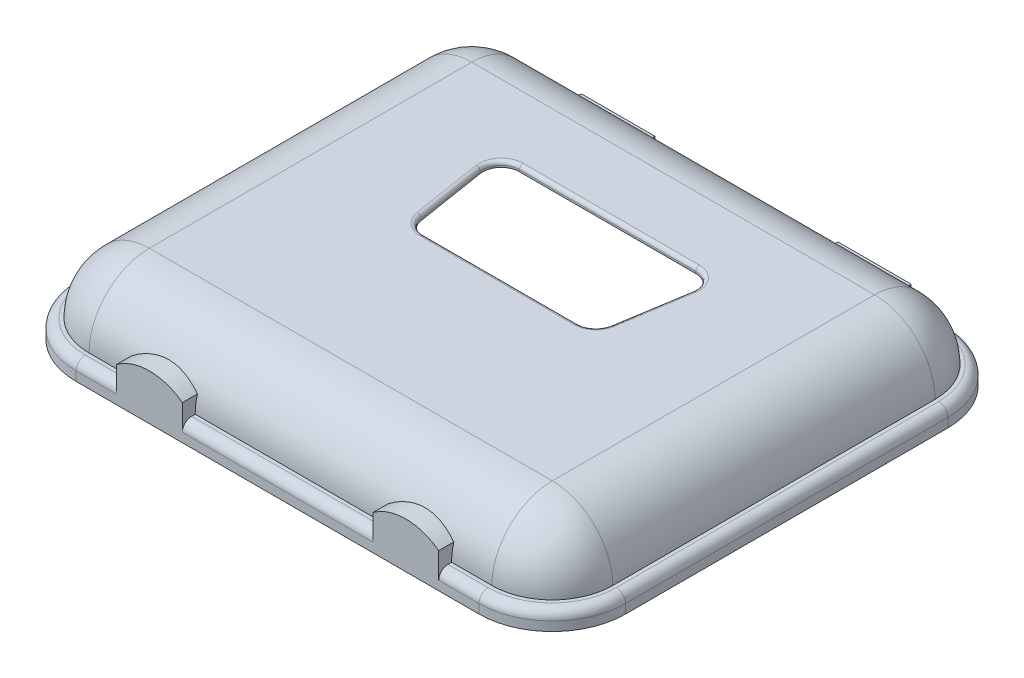
SolidWorks part; units mm, degrees
ref_plane "Front Plane" through (0, 0, 0) normal (0, 0, 1) x (1, 0, 0)
ref_plane "Top Plane" through (0, 0, 0) normal (0, 1, 0) x (1, 0, 0)
ref_plane "Right Plane" through (0, 0, 0) normal (1, 0, 0) x (0, 0, -1)
sketch "Sketch1" plane through (0, 0, 0) normal (0, 1, 0) x (1, 0, 0)
  line L1 (-118.56, 82.94) -> (167.44, 82.94)
  line L2 (-118.56, 82.94) -> (-118.56, -159.06)
  line L3 (-118.56, -159.06) -> (167.44, -159.06)
  line L4 (167.44, 82.94) -> (167.44, -159.06)
  dimension "D1" = 286
  dimension "D2" = 242
extrude "Boss-Extrude1" add sketch "Sketch1" along normal blind 43 contours L2 L3 L4 L1
fillet "Fillet1" radius 33 8 edges at (167.44, 43, 38.06) (24.44, 43, 159.06) (-118.56, 43, 38.06) (24.44, 43, -82.94) (167.44, 21.5, -82.94) (-118.56, 21.5, -82.94) (-118.56, 21.5, 159.06) (167.44, 21.5, 159.06)
shell "Shell1" thickness 3
sketch "Sketch2" plane through (0, 0, 0) normal (0, -1, 0) x (1, 0, 0)
  line L0 (-85.56, 159.06) -> (134.44, 159.06) construction
  line L1 (-85.56, 166.06) -> (134.44, 166.06)
  line L2 (-125.56, 126.06) -> (-125.56, -49.94)
  line L3 (-85.56, -89.94) -> (134.44, -89.94)
  line L4 (174.44, 126.06) -> (174.44, -49.94)
  line L5 (-118.56, -49.94) -> (-118.56, 126.06) construction
  line L6 (167.44, -49.94) -> (167.44, 126.06) construction
  line L7 (-85.56, -82.94) -> (134.44, -82.94) construction
  line L9 (-85.56, 159.06) -> (134.44, 159.06)
  line L10 (-118.56, 126.06) -> (-118.56, -49.94)
  line L11 (-85.56, -82.94) -> (134.44, -82.94)
  line L12 (167.44, 126.06) -> (167.44, -49.94)
  arc A0 (134.44, -89.94) -> (174.44, -49.94) centre (134.44, -49.94) ccw
  arc A1 (-125.56, -49.94) -> (-85.56, -89.94) centre (-85.56, -49.94) ccw
  arc A2 (134.44, 166.06) -> (174.44, 126.06) centre (134.44, 126.06) cw
  arc A3 (-85.56, 166.06) -> (-125.56, 126.06) centre (-85.56, 126.06) ccw
  arc A4 (-118.56, -49.94) -> (-85.56, -82.94) centre (-85.56, -49.94) ccw
  arc A5 (134.44, -82.94) -> (167.44, -49.94) centre (134.44, -49.94) ccw
  arc A6 (134.44, 159.06) -> (167.44, 126.06) centre (134.44, 126.06) cw
  arc A7 (-85.56, 159.06) -> (-118.56, 126.06) centre (-85.56, 126.06) ccw
  dimension "D5" = 40
  dimension "D6" = 33
  dimension "D1" = 7
  dimension "D2" = 7
  dimension "D3" = 7
  dimension "D4" = 7
extrude "Boss-Extrude2" add sketch "Sketch2" against normal blind 10
fillet "Fillet2" radius 5 8 edges at (162.7243, 10, 154.3443) (174.44, 10, 38.06) (162.7243, 10, -78.2243) (24.44, 10, -89.94) (-113.8443, 10, -78.2243) (-125.56, 10, 38.06) (-113.8443, 10, 154.3443) (24.44, 10, 166.06)
sketch "Sketch4" plane through (0, 43, 0) normal (0, 1, 0) x (1, 0, 0)
  line L0 (24.44, 14.14) -> (24.44, -44.26) construction
  line L1 (-23.6848, 14.14) -> (72.5648, 14.14)
  line L2 (-33.56, 2.5649) -> (-27.4352, -35.8351)
  line L3 (-17.56, -44.26) -> (66.44, -44.26)
  line L4 (82.44, 2.5649) -> (76.3152, -35.8351)
  line L6 (-27.4352, -35.8351) -> (76.3152, -35.8351) construction
  line L7 (24.44, -126.06) -> (24.44, 49.94) construction
  line L8 (-85.56, -126.06) -> (134.44, -126.06) construction
  line L9 (134.44, 49.94) -> (-85.56, 49.94) construction
  line L10 (-85.56, 89.94) -> (134.44, 89.94) construction
  arc A0 (-27.4352, -35.8351) -> (-17.56, -44.26) centre (-17.56, -34.26) ccw
  arc A1 (66.44, -44.26) -> (76.3152, -35.8351) centre (66.44, -34.26) ccw
  arc A2 (72.5648, 14.14) -> (82.44, 2.5649) centre (72.5648, 4.14) cw
  arc A3 (-23.6848, 14.14) -> (-33.56, 2.5649) centre (-23.6848, 4.14) ccw
  point P13 (-26.0914, -44.26)
  point P16 (74.9714, -44.26)
  point P19 (84.2862, 14.14)
  point P22 (-35.4062, 14.14)
  dimension "D4" = 10
  dimension "D1" = 84
  dimension "D2" = 116
  dimension "D3" = 58.4
  dimension "D5" = 75.8
extrude "Cut-Extrude2" cut sketch "Sketch4" against normal through all
fillet "Fillet3" radius 2 8 edges at (-24.0503, 43, 41.8676) (-30.4976, 43, 16.6351) (-31.2924, 43, -10.6303) (24.44, 43, -14.14) (80.1724, 43, -10.6303) (79.3776, 43, 16.6351) (72.9303, 43, 41.8676) (24.44, 43, 44.26)
sketch "Sketch5" plane through (0, 0, -89.94) normal (0, 0, -1) x (-1, 0, 0)
  line L0 (85.56, 0) -> (-134.44, 0) construction
  line L1 (-114.44, 0) -> (-74.44, 0)
  line L2 (-114.44, 0) -> (-114.44, 18)
  line L3 (-114.44, 18) -> (-74.44, 18)
  line L4 (-74.44, 0) -> (-74.44, 18)
  line L5 (-94.44, 18) -> (45.56, 18) construction
  line L6 (25.56, 0) -> (65.56, 0)
  line L7 (25.56, 0) -> (25.56, 18)
  line L8 (25.56, 18) -> (65.56, 18)
  line L9 (65.56, 0) -> (65.56, 18)
  line L10 (-24.44, 18) -> (-24.44, 0) construction
  dimension "D1" = 40
  dimension "D2" = 140
  dimension "D3" = 18
extrude "Boss-Extrude3" add sketch "Sketch5" against normal up to next
sketch "Sketch6" plane through (0, 0, 166.06) normal (0, 0, 1) x (1, 0, 0)
  line L0 (134.44, 0) -> (-85.56, 0) construction
  line L1 (-27.56, 0) -> (-63.56, 0)
  line L2 (-27.56, 0) -> (-27.56, 25)
  line L3 (-27.56, 25) -> (-63.56, 25)
  line L4 (-63.56, 0) -> (-63.56, 25)
  line L5 (-45.56, 25) -> (94.44, 25) construction
  line L6 (76.44, 0) -> (112.44, 0)
  line L7 (76.44, 0) -> (76.44, 25)
  line L8 (76.44, 25) -> (112.44, 25)
  line L9 (112.44, 0) -> (112.44, 25)
  line L10 (24.44, 25) -> (24.44, 0) construction
  circle A0 centre (-45.56, -5) radius 30
  circle A1 centre (94.44, -5) radius 30
  point P16 (-45.0908, 28.8434)
  point P17 (-40.3936, -6.9829)
  point P20 (94.44, -8.6059)
  point P21 (94.44, -2)
  point P22 (72.9767, -2)
  line M2 (134.44, 5) -> (-85.56, 5)
  line M4 (-85.56, 0) -> (134.44, 0)
  dimension "D4" = 60
  dimension "D1" = 140
  dimension "D2" = 36
  dimension "D3" = 25
extrude "Boss-Extrude4" add sketch "Sketch6" against normal up to next contours L4 L2 M4 M2 | L2 A0 L4 M2 | L9 A1 L7 M2 | L9 L7 M4 M2
equation "\"D2@Sketch2\"=\"D1@Sketch2\""
equation "\"D3@Sketch2\"=\"D1@Sketch2\""
equation "\"D4@Sketch2\"=\"D1@Sketch2\""
